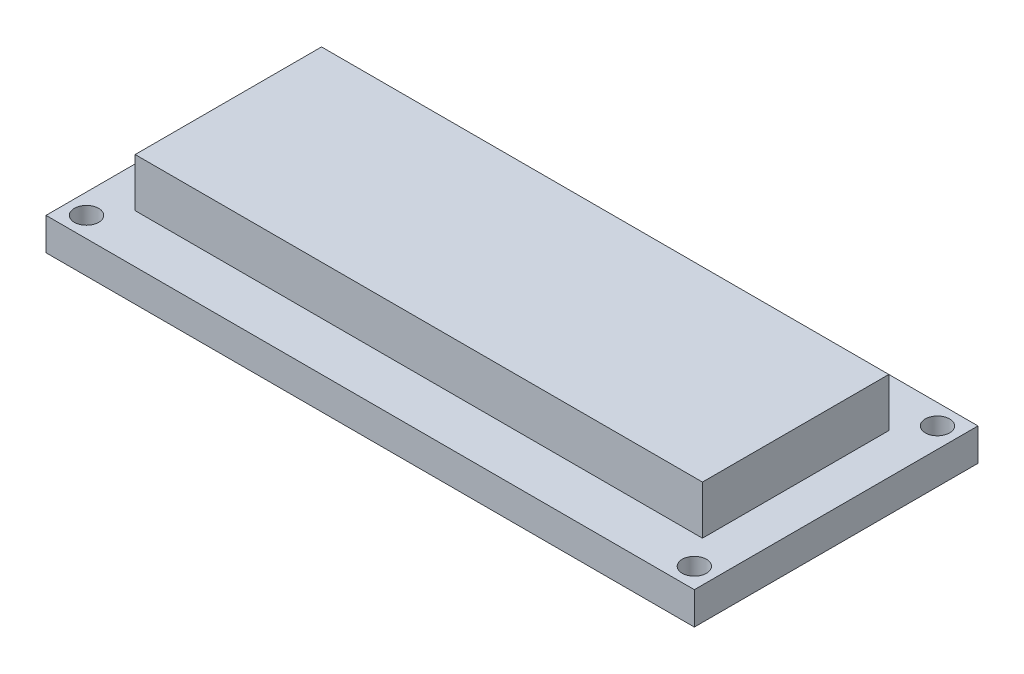
SolidWorks part; units mm, degrees
ref_plane "Płaszczyzna przednia" through (0, 0, 0) normal (0, 0, 1) x (1, 0, 0)
ref_plane "Płaszczyzna górna" through (0, 0, 0) normal (0, 1, 0) x (1, 0, 0)
ref_plane "Płaszczyzna prawa" through (0, 0, 0) normal (1, 0, 0) x (0, 0, -1)
sketch "Szkic1" plane through (0, 0, 0) normal (0, 1, 0) x (1, 0, 0)
  line L0 (0, 73.5077) -> (0, -60.0944) construction
  line L1 (40, -17.5) -> (-40, -17.5)
  line L2 (40, -17.5) -> (40, 17.5)
  line L3 (40, 17.5) -> (-40, 17.5)
  line L4 (-40, -17.5) -> (-40, 17.5)
  line L5 (40, -17.5) -> (-40, 17.5) construction
  line L6 (40, 17.5) -> (-40, -17.5) construction
  line L7 (-104.505, 0) -> (165.7863, 0) construction
  circle A0 centre (-37.5, 15) radius 1.5
  circle A1 centre (-37.5, -15) radius 1.5
  circle A2 centre (37.5, -15) radius 1.5
  circle A3 centre (37.5, 15) radius 1.5
  point P0 (0, 0)
  dimension "D3" = 3
  dimension "D1" = 2.5
  dimension "D2" = 2.5
extrude "Dodanie-wyciągnięcie1" add sketch "Szkic1" along normal blind 4
sketch "Szkic2" plane through (0, 4, 0) normal (0, 1, 0) x (1, 0, 0)
  line L1 (35, -11.5) -> (-35, -11.5)
  line L2 (35, -11.5) -> (35, 11.5)
  line L3 (35, 11.5) -> (-35, 11.5)
  line L4 (-35, -11.5) -> (-35, 11.5)
  line L5 (35, -11.5) -> (-35, 11.5) construction
  line L6 (35, 11.5) -> (-35, -11.5) construction
  point P0 (0, 0)
extrude "Dodanie-wyciągnięcie2" add sketch "Szkic2" along normal blind 6
